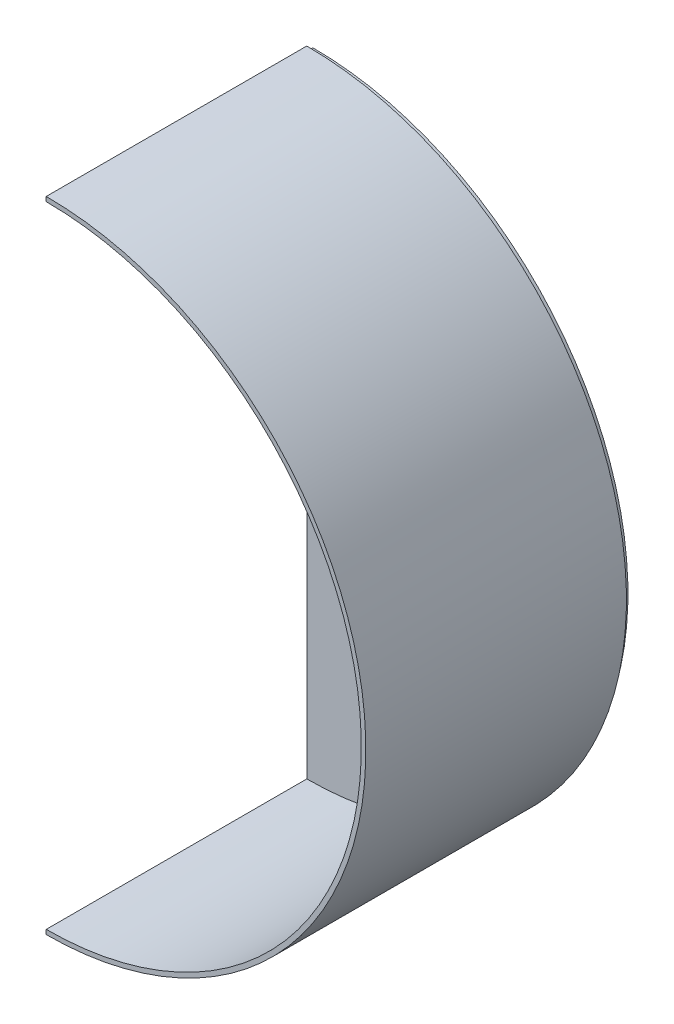
SolidWorks part; units mm, degrees
ref_plane "Front Plane" through (0, 0, 0) normal (0, 0, 1) x (1, 0, 0)
ref_plane "Top Plane" through (0, 0, 0) normal (0, 1, 0) x (1, 0, 0)
ref_plane "Right Plane" through (0, 0, 0) normal (1, 0, 0) x (0, 0, -1)
sketch "Sketch1" plane through (0, 0, 0) normal (0, 0, 1) x (1, 0, 0)
  line L0 (0, 0) -> (0, 1.5)
  line L1 (105.5, 105.5) -> (104, 105.5) construction
  line L2 (0, 209.5) -> (0, 211)
  arc A0 (0, 211) -> (0, 0) centre (0, 105.5) cw
  arc A1 (0, 209.5) -> (0, 1.5) centre (0, 105.5) cw
  dimension "D1" = 105.5
extrude "Boss-Extrude2" add sketch "Sketch1" along normal blind 86
sketch "Sketch2" plane through (0, 0, 0) normal (0, 0, -1) x (-1, 0, 0)
  line L0 (0, 0) -> (0, 80)
  line L1 (0, 131) -> (0, 211)
  line L2 (0, 131) -> (0, 80) construction
  line L3 (-32.3478, 183.1398) -> (-25.9004, 147.4559)
  line L4 (-44.6989, 126.312) -> (-76.5012, 140.4554)
  line L5 (-22.1197, 61.4335) -> (-29.549, 26.7525)
  line L6 (-46.2458, 88.3985) -> (-77.7223, 73.3509)
  arc A0 (0, 211) -> (0, 0) centre (0, 105.5) ccw
  arc A1 (0, 211) -> (0, 0) centre (0, 105.5) ccw construction
  arc A3 (-25.9004, 147.4559) -> (-44.6989, 126.312) centre (0, 105.5) ccw
  arc A4 (-32.3478, 183.1398) -> (-76.5012, 140.4554) centre (0, 105.5) ccw
  arc A5 (-46.2458, 88.3985) -> (-22.1197, 61.4335) centre (0, 105.5) ccw
  arc A6 (0, 131) -> (0, 80) centre (0, 105.5) ccw
  arc A7 (-77.7223, 73.3509) -> (-29.549, 26.7525) centre (0, 105.5) ccw
  arc M3 (0, 1.5) -> (0, 209.5) centre (0, 105.5) cw
extrude "Boss-Extrude3" add sketch "Sketch2" along normal blind 2 separate body contours A6 L1 L0 A7 L6 A5 L5 A4 L3 A3 L4 M3
